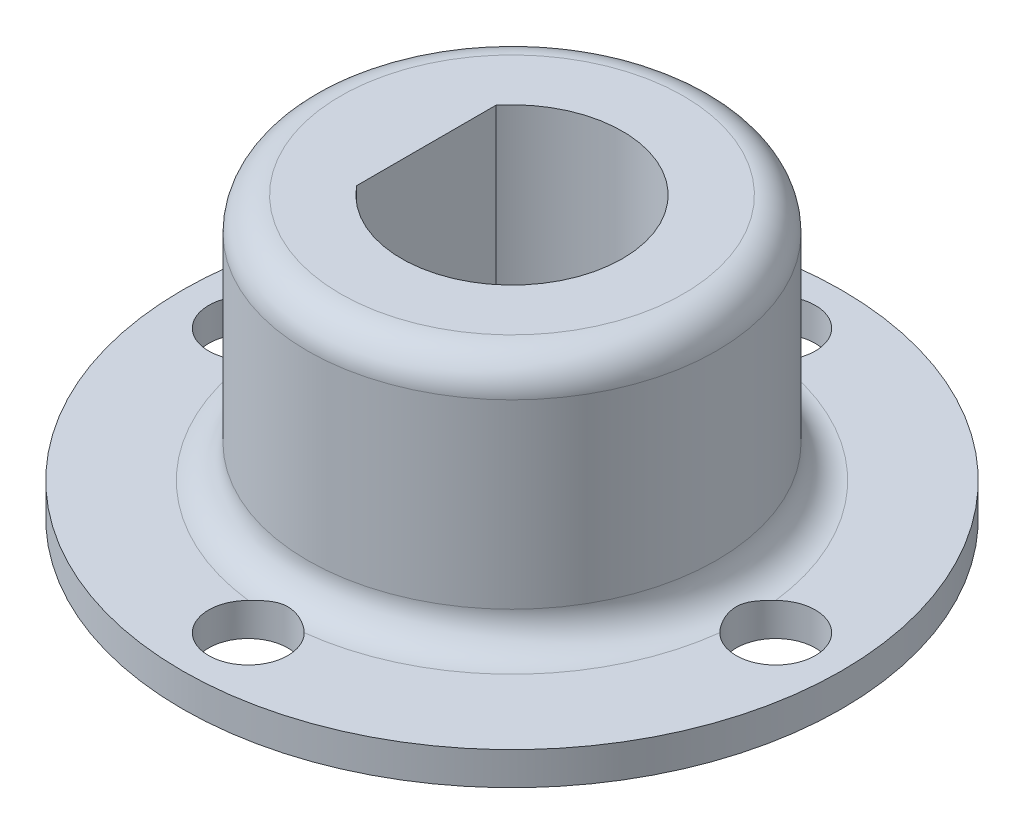
SolidWorks part; units mm, degrees
material "ABS"
ref_plane "Plan de face" through (0, 0, 0) normal (0, 0, 1) x (1, 0, 0)
ref_plane "Plan de dessus" through (0, 0, 0) normal (0, 1, 0) x (1, 0, 0)
ref_plane "Plan de droite" through (0, 0, 0) normal (1, 0, 0) x (0, 0, -1)
sketch "Sketch2" plane through (0, 0, 0) normal (0, 0, 1) x (1, 0, 0)
  line L0 (0, 0) -> (0, 8.5)
  line L1 (0, 8.5) -> (-6.2, 8.5)
  line L2 (-6.2, 8.5) -> (-6.2, 1)
  line L3 (-6.2, 1) -> (-10, 1)
  line L4 (-10, 1) -> (-10, 0)
  line L5 (-10, 0) -> (0, 0)
  dimension "D1" = 8.5
  dimension "D2" = 1
  dimension "D3" = 10
  dimension "D4" = 6.2
revolve "Revolve1" add sketch "Sketch2" angle 360 about L0
sketch "Sketch3" plane through (0, 8.5, 0) normal (0, 1, 0) x (1, 0, 0)
  line L0 (-2.6, 2.1125) -> (-2.6, -2.1125)
  arc A0 (-2.6, -2.1125) -> (-2.6, 2.1125) centre (0, 0) ccw
  dimension "D1" = 3.35
  dimension "D2" = 2.6
extrude "Cut-Extrude1" cut sketch "Sketch3" against normal blind 10
fillet "Fillet1" radius 1 2 edges at (0, 1, -6.2) (0, 8.5, -6.2)
hole_wizard "M2 Clearance Hole2" positions "Sketch6" profile "Sketch7" hole size "M2" standard "ANSI Metric" end condition through all
sketch "Sketch6" plane through (0, 0, 0) normal (0, -1, 0) x (-1, 0, 0)
  point P0 (8, 0)
  dimension "D1" = 8
sketch "Sketch7" plane through (-8, 0, 0) normal (1, 0, 0) x (0, 0, -1)
  line L0 (0, 0) -> (0, 8.5)
  line L1 (0, 8.5) -> (1.2, 8.5)
  line L2 (1.2, 8.5) -> (1.2, 0)
  line L5 (1.2, 0) -> (0, 0)
  line L11 (0, -6.35) -> (0, 107.95) construction
  dimension "Thru Hole Dia." = 2.4
  dimension "Thru Hole Depth" = 8.5
pattern_circular "CirPattern1" count 4 over 360 about axis through (0, 0, 0) along (0, 1, 0) of "M2 Clearance Hole2"
